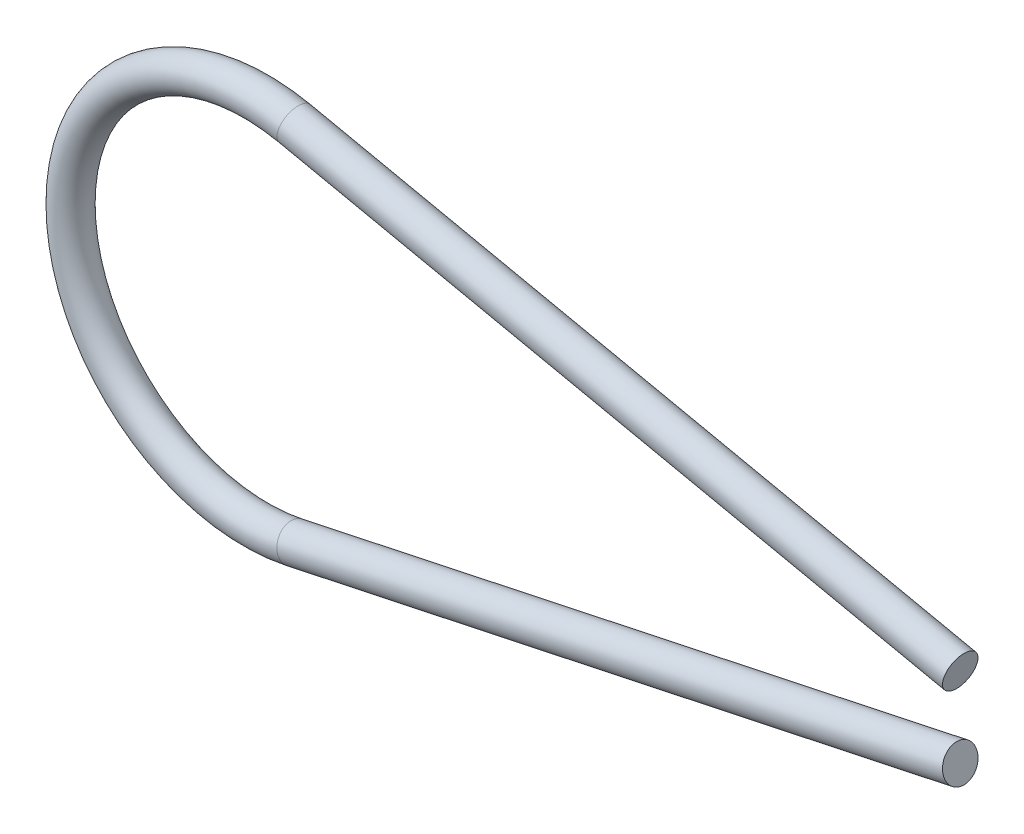
SolidWorks part; units mm, degrees
ref_plane "Alzado" through (0, 0, 0) normal (0, 0, 1) x (1, 0, 0)
ref_plane "Planta" through (0, 0, 0) normal (0, 1, 0) x (1, 0, 0)
ref_plane "Vista lateral" through (0, 0, 0) normal (1, 0, 0) x (0, 0, -1)
sketch "Sketch1" plane through (0, 0, 0) normal (0, 0, 1) x (1, 0, 0)
  line L0 (-1000, 0) -> (49000, 0) construction
  line L1 (3.2155, 0.9523) -> (48910.5956, -10394.6323) construction
  line L2 (4.6598, -0.6453) -> (-48902.7202, -10396.2298) construction
  line L3 (6.0744, -0.3446) -> (0.3327, -1.565)
  line L4 (6.0744, 0.3446) -> (0.3327, 1.565)
  arc A0 (0.3327, 1.565) -> (0.3327, -1.565) centre (0, 0) ccw
  circle A1 centre (7.6956, 0) radius 1.6574 construction
  point P9 (7.6956, 0)
  point P10 (6.0744, 0.3446)
  point P14 (6.0744, -0.3446)
  dimension "D1" = 1.6
  dimension "D2" = 12
  dimension "D3" = 5.87
curve "CompCurve1"
ref_plane "Plane1" through (6.0744, 0.3446, 0) normal (-0.9781, 0.2079, 0) x (0, 0, 1)
sketch "Sketch2" plane through (6.0744, 0.3446, 0) normal (-0.9781, 0.2079, 0) x (0, 0, 1)
  circle A0 centre (0, 0) radius 0.15
  point P0 (0, 0)
  dimension "D1" = 0.3
sweep "Sweep1" add profiles "Sketch2" path "CompCurve1"
